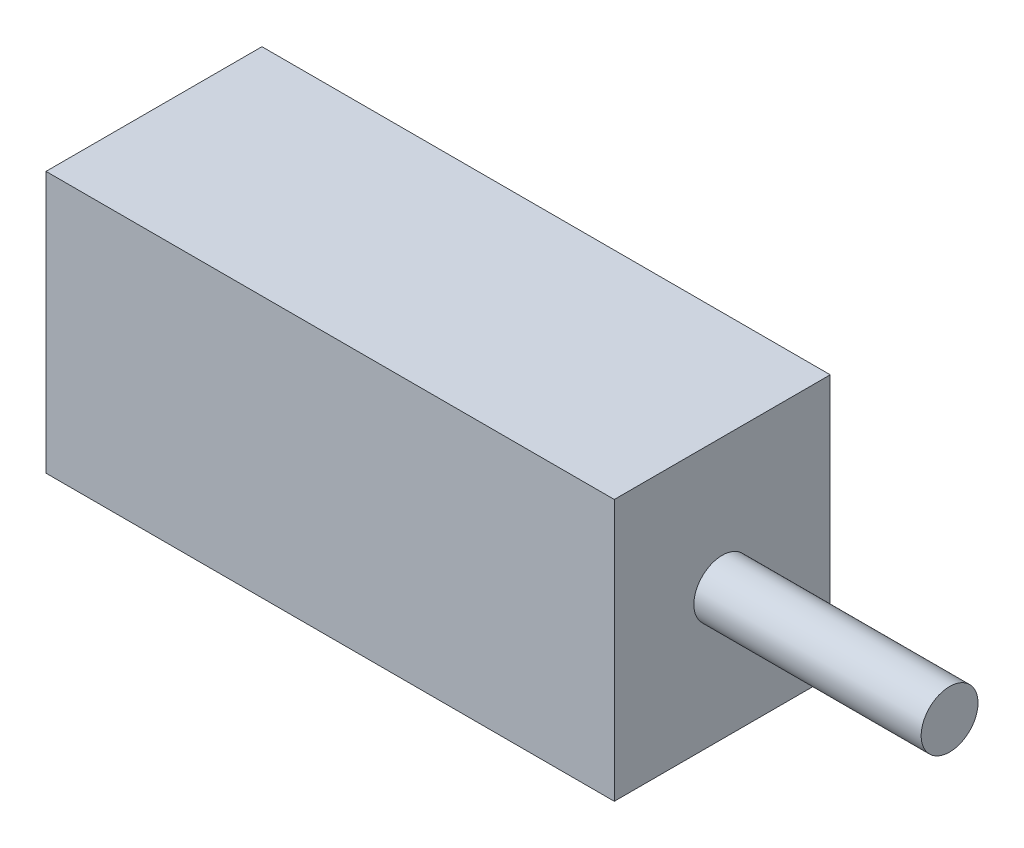
SolidWorks part; units mm, degrees
ref_plane "Front Plane" through (0, 0, 0) normal (0, 0, 1) x (1, 0, 0)
ref_plane "Top Plane" through (0, 0, 0) normal (0, 1, 0) x (1, 0, 0)
ref_plane "Right Plane" through (0, 0, 0) normal (1, 0, 0) x (0, 0, -1)
sketch "Sketch1" plane through (0, 0, 0) normal (1, 0, 0) x (0, 0, -1)
  circle A0 centre (0, 0) radius 1.25
  dimension "D1" = 2.5
extrude "Boss-Extrude1" add sketch "Sketch1" along normal blind 10
sketch "Sketch2" plane through (0, 0, 0) normal (-1, 0, 0) x (0, 0, 1)
  line L1 (-4.75, 5.75) -> (4.75, 5.75)
  line L2 (-4.75, 5.75) -> (-4.75, -5.75)
  line L3 (-4.75, -5.75) -> (4.75, -5.75)
  line L4 (4.75, 5.75) -> (4.75, -5.75)
  line L5 (-4.75, 5.75) -> (4.75, -5.75) construction
  line L6 (-4.75, -5.75) -> (4.75, 5.75) construction
  point P0 (0, 0)
  dimension "D1" = 11.5
  dimension "D2" = 9.5
extrude "Boss-Extrude2" add sketch "Sketch2" along normal blind 25
